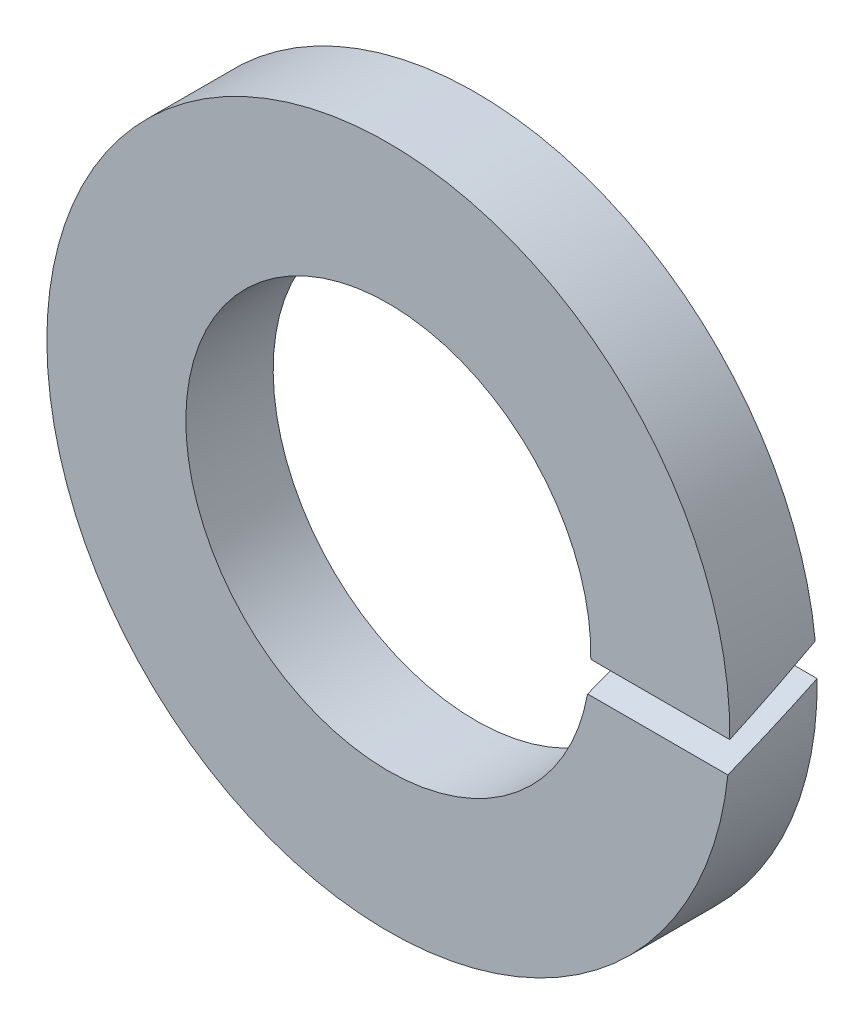
SolidWorks part; units mm, degrees
ref_plane "Přední rovina" through (0, 0, 0) normal (0, 0, 1) x (1, 0, 0)
ref_plane "Vrchní rovina" through (0, 0, 0) normal (0, 1, 0) x (1, 0, 0)
ref_plane "Pravá rovina" through (0, 0, 0) normal (1, 0, 0) x (0, 0, -1)
sketch "Skica1" plane through (0, 0, 0) normal (0, 0, 1) x (1, 0, 0)
  circle A0 centre (0, 0) radius 5.1
  circle A1 centre (0, 0) radius 8.6
  dimension "d1" = 10.2
  dimension "d2" = 17.2
extrude "Vysunout1" add sketch "Skica1" along normal blind 2.2
fillet "Zaoblit1" [suppressed] radius 0.6
sketch "Skica2" plane through (0, 0, 0) normal (1, 0, 0) x (0, 0, -1)
  line L0 (0, 0) -> (-2.2, 0) construction
  line L1 (-2.2, 8.6) -> (-2.2, -8.6) construction
  line L2 (0, 0.1157) -> (-2.2, -0.9102)
  line L3 (0, -8.6) -> (0, 8.6) construction
  line L4 (0, 0.9102) -> (-2.2, -0.1157)
  line L5 (0, 0.1157) -> (0, 0.9102)
  line L6 (-2.2, -0.9102) -> (-2.2, -0.1157)
  line L7 (0, 0.9102) -> (0, 0) construction
  line L8 (-2.2, 0) -> (-2.2, -0.9102) construction
  dimension "D1" = 65
  dimension "D2" = 0.72
extrude "Odebrat vysunutím1" cut sketch "Skica2" along normal through all
equation "\"D2@Skica2\" = \"R@Zaoblit1\" * 1.2"
